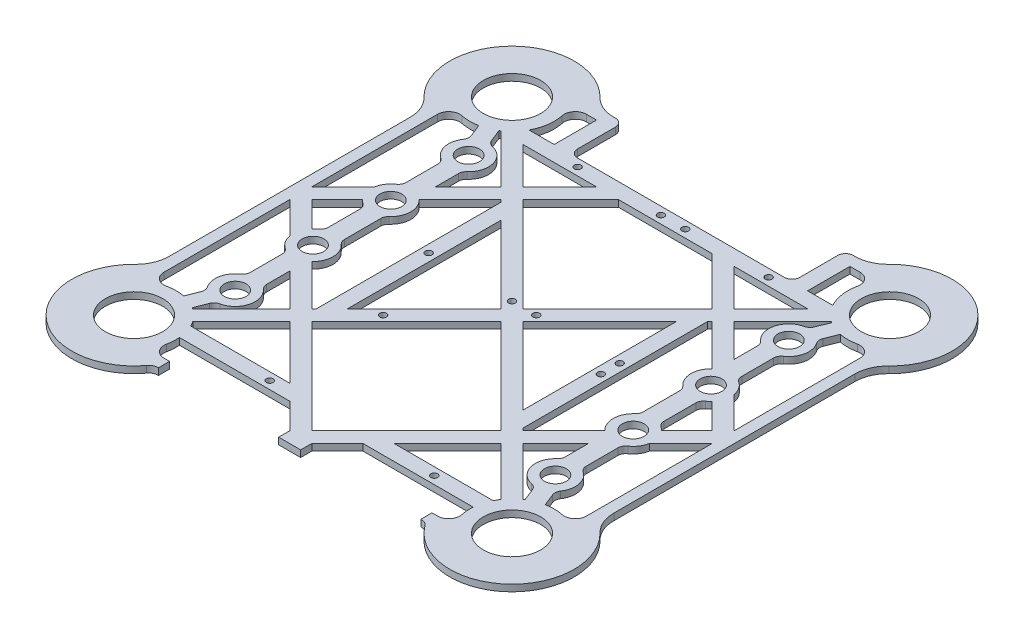
SolidWorks part; units mm, degrees
material "Acrylic (Medium-high impact)"
ref_plane "Front Plane" through (0, 0, 0) normal (0, 0, 1) x (1, 0, 0)
ref_plane "Top Plane" through (0, 0, 0) normal (0, 1, 0) x (1, 0, 0)
ref_plane "Right Plane" through (0, 0, 0) normal (1, 0, 0) x (0, 0, -1)
sketch "Sketch1" plane through (0, 0, 0) normal (0, 1, 0) x (1, 0, 0)
  line L0 (47.5, 52.4498) -> (64.0103, 68.96)
  line L1 (100, 54.1942) -> (100, -54.1941)
  line L2 (0, -55) -> (0, 55) construction
  line L3 (53.5, 100) -> (54.1942, 100)
  line L4 (4.9497, 0) -> (39.46, -34.5103)
  line L5 (0, -100) -> (4.9498, -100)
  line L6 (30.9898, 68.96) -> (64.0103, 68.96)
  line L7 (57, 95) -> (61.5266, 95)
  line L8 (95, 61.5266) -> (95, 4.9498)
  line L9 (59, -95) -> (61.5266, -95)
  line L10 (0, -90.0503) -> (0, -100)
  line L11 (0, -4.9497) -> (42.5503, -47.5)
  line L12 (85, 85) -> (0, 0) construction
  line L13 (0, 0) -> (85, -85) construction
  line L14 (0, -95) -> (95, 0) construction
  line L15 (22.54, 72.46) -> (95, 0) construction
  line L16 (57, 75.96) -> (68.2884, 75.96)
  line L17 (21.0902, 68.96) -> (42.5502, 47.5)
  line L18 (0, 4.9497) -> (42.5502, 47.5)
  line L19 (4.9497, 0) -> (39.46, 34.5103)
  line L20 (0, 4.9497) -> (0, -4.9497)
  line L21 (0, -90.0503) -> (42.5503, -47.5)
  line L22 (95, -4.9497) -> (52.4498, -47.5)
  line L23 (47.5, -52.4497) -> (69.32, -74.2698)
  line L24 (0, 72.46) -> (70.726, 72.46) construction
  line L25 (0, 75.96) -> (46.5, 75.96)
  line L26 (0, 68.96) -> (21.0902, 68.96)
  line L27 (50, 96.5) -> (50, 79.46)
  line L28 (57, 95) -> (57, 75.96)
  line L29 (30.9898, 68.96) -> (47.5, 52.4498)
  line L30 (0, 75.96) -> (0, 68.96)
  line L31 (47.5, -52.4497) -> (23.4498, -76.5)
  line L32 (95, -4.9497) -> (95, -61.5266)
  line L33 (52.4498, -47.5) -> (74.2698, -69.32)
  line L34 (47.5, -42.5502) -> (90.0503, 0)
  line L35 (47.5, 42.5503) -> (90.0503, 0)
  line L36 (52.4498, 47.5) -> (74.2698, 69.32)
  line L37 (52.4498, 47.5) -> (95, 4.9498)
  line L38 (42.96, 42.96) -> (42.96, -42.96) construction
  line L39 (39.46, 34.5103) -> (39.46, -34.5103)
  line L40 (46.46, 41.5103) -> (46.46, -41.5103)
  line L41 (46.46, 41.5103) -> (47.5, 42.5503)
  line L42 (46.46, -41.5103) -> (47.5, -42.5502)
  line L43 (5.46, 5.46) -> (5.46, 72.46) construction
  line L44 (5.46, 5.46) -> (42.96, 5.46) construction
  line L45 (23.4498, -76.5) -> (68.0074, -76.5)
  line L46 (16.4498, -83.5) -> (66.0593, -83.5)
  line L47 (16.4498, -83.5) -> (4.9498, -95)
  line L48 (15, -80) -> (73.1084, -80) construction
  line L49 (4.9498, -95) -> (4.9498, -100)
  line L50 (59, -95) -> (59, -100)
  circle A0 centre (85, 85) radius 12.9
  arc A1 (104.5349, 64.9404) -> (64.9404, 104.5349) centre (85, 85) ccw
  arc A2 (100, 54.1942) -> (104.5349, 64.9404) centre (115, 54.1942) cw
  arc A3 (54.1942, 100) -> (64.9404, 104.5349) centre (54.1942, 115) ccw
  circle A4 centre (85, -85) radius 12.9
  arc A5 (62.6, -101.8) -> (104.5349, -64.9404) centre (85, -85) ccw
  arc A6 (100, -54.1941) -> (104.5349, -64.9404) centre (115, -54.1941) ccw
  arc A7 (59, -100) -> (62.6, -101.8) centre (59.1514, -104.1973) cw
  arc A8 (66.4169, 88.9583) -> (68.2884, 75.96) centre (85, 85) ccw
  arc A9 (95, 61.5266) -> (88.9583, 66.4169) centre (90, 61.5266) ccw
  arc A10 (61.5266, 95) -> (66.4169, 88.9583) centre (61.5266, 90) cw
  arc A11 (88.9583, -66.4169) -> (74.2698, -69.32) centre (85, -85) ccw
  arc A12 (95, -61.5266) -> (88.9583, -66.4169) centre (90, -61.5266) cw
  arc A13 (61.5266, -95) -> (66.4169, -88.9583) centre (61.5266, -90) ccw
  arc A14 (74.2698, 69.32) -> (88.9583, 66.4169) centre (85, 85) ccw
  arc A15 (69.32, -74.2698) -> (68.0074, -76.5) centre (85, -85) ccw
  arc A16 (50, 79.46) -> (46.5, 75.96) centre (46.5, 79.46) cw
  arc A17 (50, 96.5) -> (53.5, 100) centre (53.5, 96.5) cw
  circle A18 centre (5.46, 5.46) radius 1.5
  circle A19 centre (5.46, 72.46) radius 1.5
  circle A20 centre (42.96, 5.46) radius 1.5
  circle A21 centre (42.96, 72.46) radius 1.5
  arc A22 (66.0593, -83.5) -> (66.4169, -88.9583) centre (85, -85) ccw
  dimension "D2" = 25.8
  dimension "D6" = 28
  dimension "D7" = 15
  dimension "D9" = 19
  dimension "D10" = 10
  dimension "D13" = 15
  dimension "D14" = 59
  dimension "D15" = 5
  dimension "D18" = 5
  dimension "D20" = 5
  dimension "D11" = 3.5
  dimension "D21" = 3.5
  dimension "D37" = 3
  dimension "D12" = 4.2
  dimension "D1" = 100
  dimension "D3" = 15
  dimension "D4" = 15
  dimension "D5" = 200
  dimension "D8" = 15
  dimension "D16" = 5
  dimension "D17" = 5
  dimension "D22" = 3.5
  dimension "D23" = 3.5
  dimension "D24" = 37.5
  dimension "D25" = 3.5
  dimension "D26" = 3.5
  dimension "D27" = 3.5
  dimension "D28" = 3.5
  dimension "D29" = 5
  dimension "D30" = 27.54
  dimension "D31" = 3.5
  dimension "D32" = 3.5
  dimension "D33" = 7
  dimension "D34" = 50
  dimension "D35" = 3.5
  dimension "D36" = 3.5
  dimension "D38" = 67
  dimension "D39" = 7
  dimension "D40" = 3.5
  dimension "D41" = 20
extrude "Boss-Extrude1" add sketch "Sketch1" along normal blind 3
sketch "Sketch2" plane through (0, 3, 0) normal (0, 1, 0) x (1, 0, 0)
  line L0 (72.0096, 52.5) -> (72.0096, -52.5) construction
  line L1 (95, 61.5266) -> (95, 4.9498) construction
  line L2 (72.0096, 52.5) -> (85, 85) construction
  line L3 (85, -85) -> (72.0096, -52.5) construction
  circle A0 centre (85, 85) radius 17.5
  circle A1 centre (72.0096, 52.5) radius 17.5
  circle A2 centre (85, -85) radius 17.5
  circle A3 centre (72.0096, 17.5) radius 17.5
  circle A4 centre (72.0096, -17.5) radius 17.5
  circle A5 centre (72.0096, -52.5) radius 17.5
  dimension "D1" = 35
sketch "Sketch3" plane through (0, 0, 0) normal (0, 1, 0) x (1, 0, 0)
  line L0 (81.3188, -66.36) -> (79.1033, -60.8174)
  line L1 (85, -85) -> (72.0096, -52.5) construction
  line L2 (74.8188, -68.9581) -> (72.6033, -63.4155)
  line L3 (75.5096, -42.1438) -> (75.5096, -27.8561)
  line L4 (72.0096, 52.5) -> (72.0096, -52.5) construction
  line L5 (67.1763, -26.8169) -> (67.1763, -43.183)
  line L6 (74.8188, 68.9581) -> (72.6033, 63.4155)
  line L7 (81.3188, 66.36) -> (79.1033, 60.8174)
  line L8 (72.0096, 52.5) -> (85, 85) construction
  line L9 (67.1763, 8.1831) -> (67.1763, -8.183)
  line L10 (75.5096, 27.8562) -> (75.5096, 42.1439)
  line L11 (75.5096, -7.1438) -> (75.5096, 7.1439)
  line L12 (67.1763, 43.1831) -> (67.1763, 26.817)
  arc A0 (74.8188, 68.9581) -> (81.3188, 66.36) centre (85, 85) ccw
  arc A1 (66.0096, -10.7918) -> (66.0096, -24.2082) centre (72.0096, -17.5) ccw
  arc A2 (66.0096, 24.2082) -> (66.0096, 10.7918) centre (72.0096, 17.5) ccw
  circle A3 centre (72.0096, 17.5) radius 4.9
  arc A4 (77.0496, 10.0436) -> (77.0496, 24.9564) centre (72.0096, 17.5) ccw
  arc A5 (66.0096, 24.2082) -> (67.1763, 26.817) centre (63.6763, 26.817) ccw
  arc A6 (67.1763, 8.1831) -> (66.0096, 10.7918) centre (63.6763, 8.1831) ccw
  arc A7 (75.5096, 7.1439) -> (77.0496, 10.0436) centre (79.0096, 7.1439) cw
  arc A8 (77.0496, 24.9564) -> (75.5096, 27.8562) centre (79.0096, 27.8562) cw
  arc A9 (66.0096, -24.2082) -> (67.1763, -26.8169) centre (63.6763, -26.8169) cw
  arc A10 (79.1033, 60.8174) -> (79.4571, 57.5532) centre (82.3533, 59.5184) ccw
  arc A11 (81.3188, -66.36) -> (74.8188, -68.9581) centre (85, -85) ccw
  arc A12 (66.0096, -45.7918) -> (70.0971, -61.2944) centre (72.0096, -52.5) ccw
  arc A13 (70.0971, 61.2945) -> (66.0096, 45.7918) centre (72.0096, 52.5) ccw
  circle A14 centre (72.0096, -17.5) radius 4.9
  circle A15 centre (72.0096, -52.5) radius 4.9
  circle A16 centre (72.0096, 52.5) radius 4.9
  arc A17 (79.4571, -57.5532) -> (77.0496, -45.0436) centre (72.0096, -52.5) ccw
  arc A18 (77.0496, -24.9564) -> (77.0496, -10.0436) centre (72.0096, -17.5) ccw
  arc A19 (77.0496, 45.0436) -> (79.4571, 57.5532) centre (72.0096, 52.5) ccw
  arc A20 (70.0971, 61.2945) -> (72.6033, 63.4155) centre (69.3533, 64.7145) ccw
  arc A21 (66.0096, 45.7918) -> (67.1763, 43.1831) centre (63.6763, 43.1831) cw
  arc A22 (77.0496, 45.0436) -> (75.5096, 42.1439) centre (79.0096, 42.1439) ccw
  arc A23 (79.4571, -57.5532) -> (79.1033, -60.8174) centre (82.3533, -59.5183) ccw
  arc A24 (70.0971, -61.2944) -> (72.6033, -63.4155) centre (69.3533, -64.7145) cw
  arc A25 (66.0096, -45.7918) -> (67.1763, -43.183) centre (63.6763, -43.183) ccw
  arc A26 (75.5096, -42.1438) -> (77.0496, -45.0436) centre (79.0096, -42.1438) ccw
  arc A27 (77.0496, -24.9564) -> (75.5096, -27.8561) centre (79.0096, -27.8561) ccw
  arc A28 (75.5096, -7.1438) -> (77.0496, -10.0436) centre (79.0096, -7.1438) ccw
  arc A29 (66.0096, -10.7918) -> (67.1763, -8.183) centre (63.6763, -8.183) ccw
  point P13 (67.1763, -25.092)
  point P31 (75.5096, 9.2084)
  point P34 (75.5096, 25.7916)
  point P69 (67.1763, -44.908)
  point P76 (75.5096, -9.2084)
  dimension "D6" = 19
  dimension "D9" = 18
  dimension "D10" = 9.8
  dimension "D11" = 3.5
  dimension "D12" = 19
  dimension "D5" = 3.5
  dimension "D2" = 3.5
  dimension "D3" = 3.5
  dimension "D4" = 3.5
  dimension "D7" = 3.5
  dimension "D8" = 3.5
extrude "Boss-Extrude2" add sketch "Sketch3" along normal blind 3
sketch "Sketch5" plane through (0, 0, 0) normal (0, 1, 0) x (1, 0, 0)
  circle A0 centre (72.0096, 17.5) radius 4.9
  circle A1 centre (72.0096, -17.5) radius 4.9
  arc A2 (68.8257, 21.2246) -> (75.7342, 14.3161) centre (72.0096, 17.5) ccw construction
extrude "Cut-Extrude2" cut sketch "Sketch5" along normal blind 3
mirror "Mirror2" about plane through (0, 0, 0) normal (1, 0, 0) of "Cut-Extrude2", "Boss-Extrude2", "Boss-Extrude1"
sketch "Sketch6" plane through (0, 3, 0) normal (0, 1, 0) x (1, 0, 0)
  line L0 (-28.9862, -79.9861) -> (45.0138, -79.9861) construction
  line L1 (59, -95) -> (61.5266, -95) construction
  line L2 (-28.9862, -79.9861) -> (-28.9862, -28.9861) construction
  line L3 (-4.9497, 0) -> (-39.46, -34.5103) construction
  line L5 (-4.9498, -100) -> (4.9498, -100) construction
  circle A0 centre (45.0138, -79.9861) radius 1.5
  circle A1 centre (42.96, -2.9861) radius 1.5
  circle A2 centre (42.96, 5.46) radius 1.5
  circle A3 centre (42.96, 5.46) radius 1.5 construction
  circle A4 centre (-28.9862, -79.9861) radius 1.5
  circle A5 centre (-28.9862, -28.9861) radius 1.5
  dimension "D1" = 3.5
  dimension "D2" = 77
  dimension "D3" = 74
  dimension "D5" = 76.5
extrude "Cut-Extrude3" cut sketch "Sketch6" against normal blind 3 contours A5 | A1 | A4 | A0
